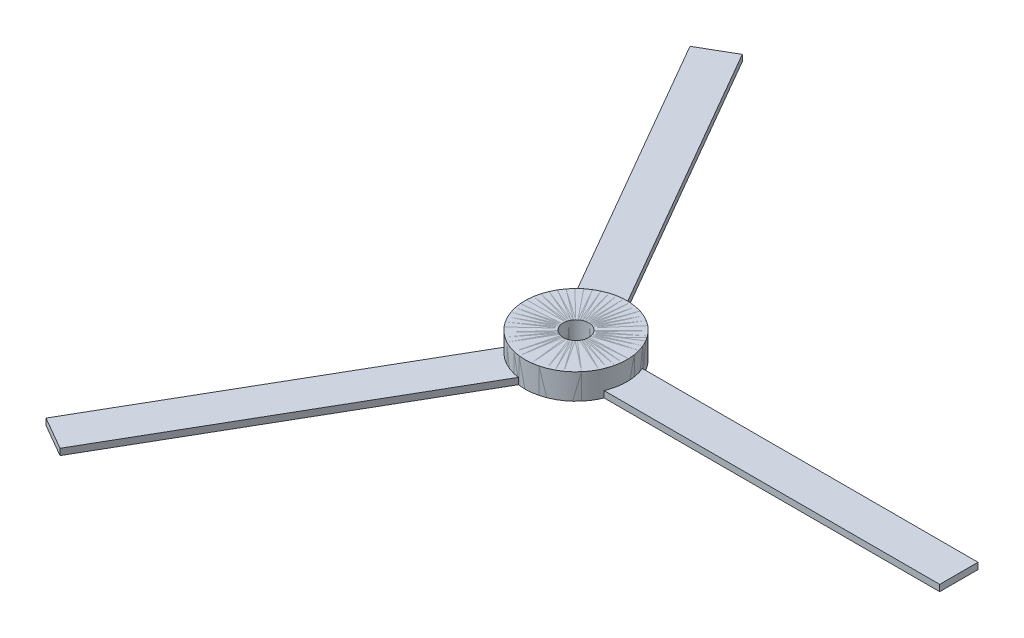
SolidWorks part; units mm, degrees
ref_plane "Front Plane" through (0, 0, 0) normal (0, 0, 1) x (1, 0, 0)
ref_plane "Top Plane" through (0, 0, 0) normal (0, 1, 0) x (1, 0, 0)
ref_plane "Right Plane" through (0, 0, 0) normal (1, 0, 0) x (0, 0, -1)
sketch "Sketch1" plane through (0, 0, 0) normal (0, 1, 0) x (1, 0, 0)
  circle A0 centre (0, 0) radius 1
  circle A1 centre (0, 0) radius 4
  dimension "D1" = 2
  dimension "D2" = 3
extrude "Boss-Extrude1" add sketch "Sketch1" along normal blind 2
sketch "Sketch2" plane through (0, 2, 0) normal (0, 1, 0) x (1, 0, 0)
  line L5 (-1, -0.6) -> (-1, 0.6)
  line L8 (-1, 0.6) -> (-29, 0.6)
  line L9 (-29, 0.6) -> (-29, -0.6)
  line L10 (-29, -0.6) -> (-1, -0.6)
  circle A0 centre (0, 0) radius 1 construction
  point P3 (-1, 0)
  point P18 (0, 0)
  dimension "D1" = 28
  dimension "D2" = 1.2
pattern_circular "CirPattern2" count 3 over 360 about axis through (0, 2, 0) along (0, 1, 0) of bodies 101 104
extrude "Boss-Extrude4" [suppressed] add sketch "Sketch2" against normal blind 1
sketch "Sketch4" [suppressed] plane through (-29, 0, 0) normal (-1, 0, 0) x (0, 0, 1)
  line L0 (-0.6, 1.5) -> (0, 2)
  line L1 (-0.6, 1) -> (-0.6, 2) construction
  line L2 (-0.6, 2) -> (0.6, 2) construction
  line L3 (0, 2) -> (0.6, 1.5)
  line L4 (0.6, 1) -> (0.6, 2) construction
  line L5 (0.6, 1.5) -> (0, 1)
  line L6 (-0.6, 1) -> (0.6, 1) construction
  line L7 (0, 1) -> (-0.6, 1.5)
pattern_circular "CirPattern3" [suppressed] count 3 over 360
sketch "Sketch5" plane through (0, 2, 0) normal (0, 1, 0) x (1, 0, 0)
  line L0 (0, 0) -> (30, 0) construction
  line L1 (0, 1.5) -> (30, 1.5)
  line L2 (0, -1.5) -> (30, -1.5)
  line L3 (30, -1.5) -> (30, 1.5)
  line L4 (0, 1.5) -> (0, -1.5)
  dimension "D3" = 30
  dimension "D1" = 1.5
  dimension "D2" = 1.5
extrude "Boss-Extrude5" add sketch "Sketch5" along normal blind 0.5 from surface at -2 separate body starting at face at (0, 0, 4)
pattern_circular "CirPattern4" count 3 over 360 about axis through (0, 0, 0) along (0, 1, 0) of bodies 111
sketch "Sketch6" plane through (0, 2, 0) normal (0, 1, 0) x (1, 0, 0)
  circle A0 centre (0, 0) radius 1
  dimension "D1" = 2
extrude "Cut-Extrude1" cut sketch "Sketch6" against normal blind 10
